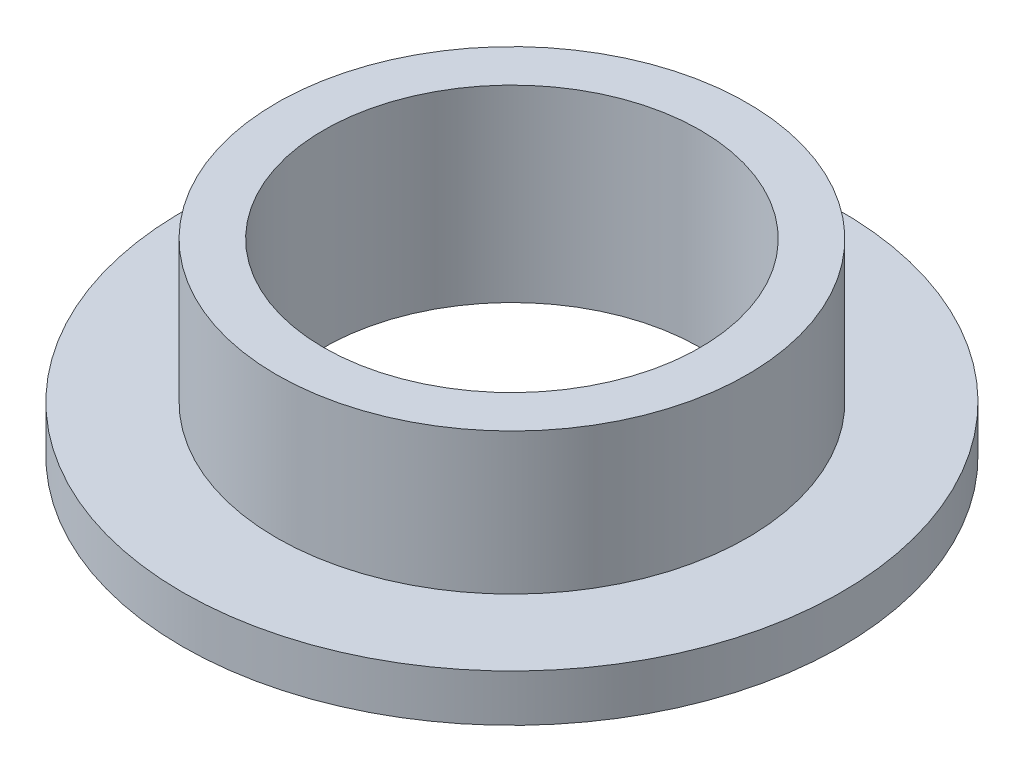
SolidWorks part; units mm, degrees
ref_plane "Front" through (0, 0, 0) normal (0, 0, 1) x (1, 0, 0)
ref_plane "Top" through (0, 0, 0) normal (0, 1, 0) x (1, 0, 0)
ref_plane "Right" through (0, 0, 0) normal (1, 0, 0) x (0, 0, -1)
sketch "Sketch1" plane through (0, 0, 0) normal (0, 1, 0) x (1, 0, 0)
  circle A0 centre (0, 0) radius 6.35
  circle A1 centre (0, 0) radius 7.9375
  circle A2 centre (0, 0) radius 11.1125
  dimension "ID" = 12.7
  dimension "OD" = 15.875
  dimension "FlangeOD" = 22.225
sketch "Sketch2" plane through (0, 0, 0) normal (0, 1, 0) x (1, 0, 0)
  circle A0 centre (0, 0) radius 6.35 construction
  circle A1 centre (0, 0) radius 7.9375 construction
  circle A2 centre (0, 0) radius 6.35
  circle A3 centre (0, 0) radius 7.9375
extrude "Boss-Extrude1" add sketch "Sketch2" along normal blind 6.35
sketch "Sketch3" plane through (0, 0, 0) normal (0, 1, 0) x (1, 0, 0)
  circle A0 centre (0, 0) radius 11.1125 construction
  circle A1 centre (0, 0) radius 7.9375 construction
  circle A2 centre (0, 0) radius 11.1125
  circle A3 centre (0, 0) radius 7.9375
extrude "Boss-Extrude2" add sketch "Sketch3" along normal blind 1.5875
